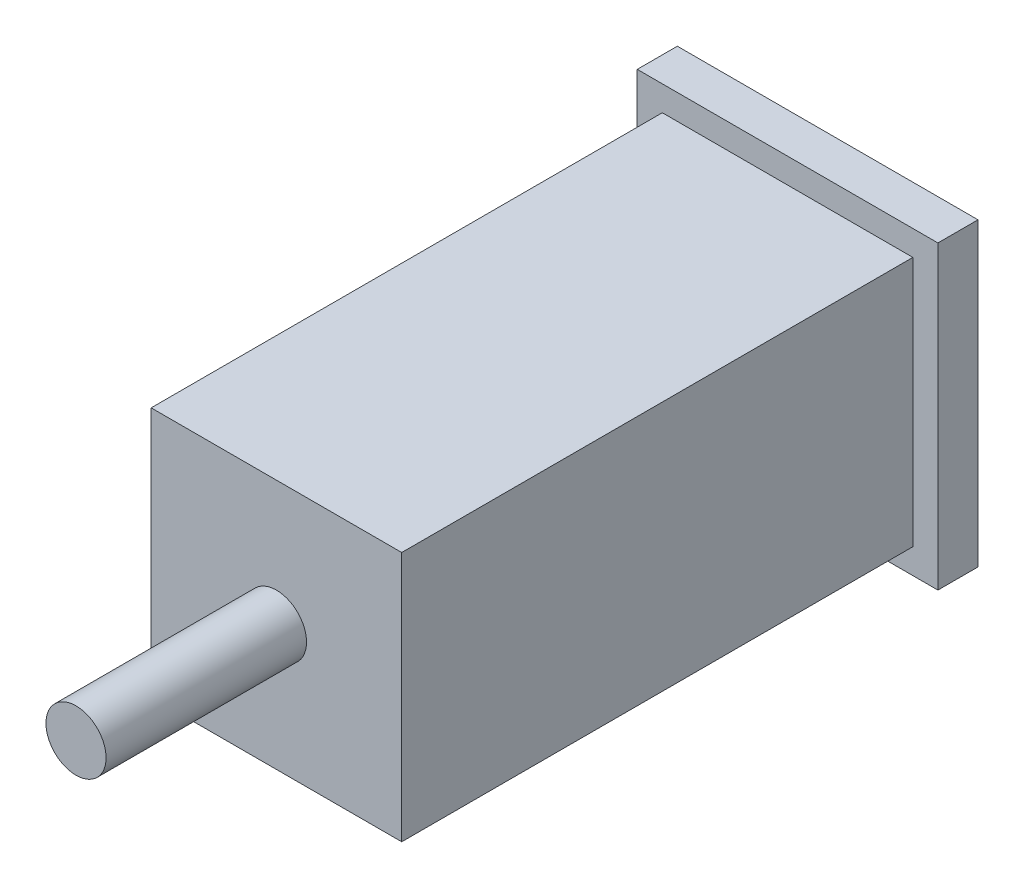
SolidWorks part; units mm, degrees
ref_plane "Front Plane" through (0, 0, 0) normal (0, 0, 1) x (1, 0, 0)
ref_plane "Top Plane" through (0, 0, 0) normal (0, 1, 0) x (1, 0, 0)
ref_plane "Right Plane" through (0, 0, 0) normal (1, 0, 0) x (0, 0, -1)
sketch "Sketch1" plane through (0, 0, 0) normal (0, 0, 1) x (1, 0, 0)
  line L1 (-15, -15) -> (15, -15)
  line L2 (-15, -15) -> (-15, 15)
  line L3 (-15, 15) -> (15, 15)
  line L4 (15, -15) -> (15, 15)
  line L5 (-15, -15) -> (15, 15) construction
  line L6 (-15, 15) -> (15, -15) construction
  point P0 (0, 0)
  dimension "D1" = 30
  dimension "D2" = 30
extrude "Boss-Extrude1" add sketch "Sketch1" along normal blind 4
sketch "Sketch2" plane through (0, 0, 4) normal (0, 0, 1) x (1, 0, 0)
  line L1 (-12.5, -12.5) -> (12.5, -12.5)
  line L2 (-12.5, -12.5) -> (-12.5, 12.5)
  line L3 (-12.5, 12.5) -> (12.5, 12.5)
  line L4 (12.5, -12.5) -> (12.5, 12.5)
  line L5 (-12.5, -12.5) -> (12.5, 12.5) construction
  line L6 (-12.5, 12.5) -> (12.5, -12.5) construction
  point P0 (0, 0)
  dimension "D1" = 25
  dimension "D2" = 25
extrude "Boss-Extrude2" add sketch "Sketch2" along normal blind 51
sketch "Sketch3" plane through (0, 0, 55) normal (0, 0, 1) x (1, 0, 0)
  circle A0 centre (0, 0) radius 3
  dimension "D1" = 6
extrude "Boss-Extrude3" add sketch "Sketch3" along normal blind 20
